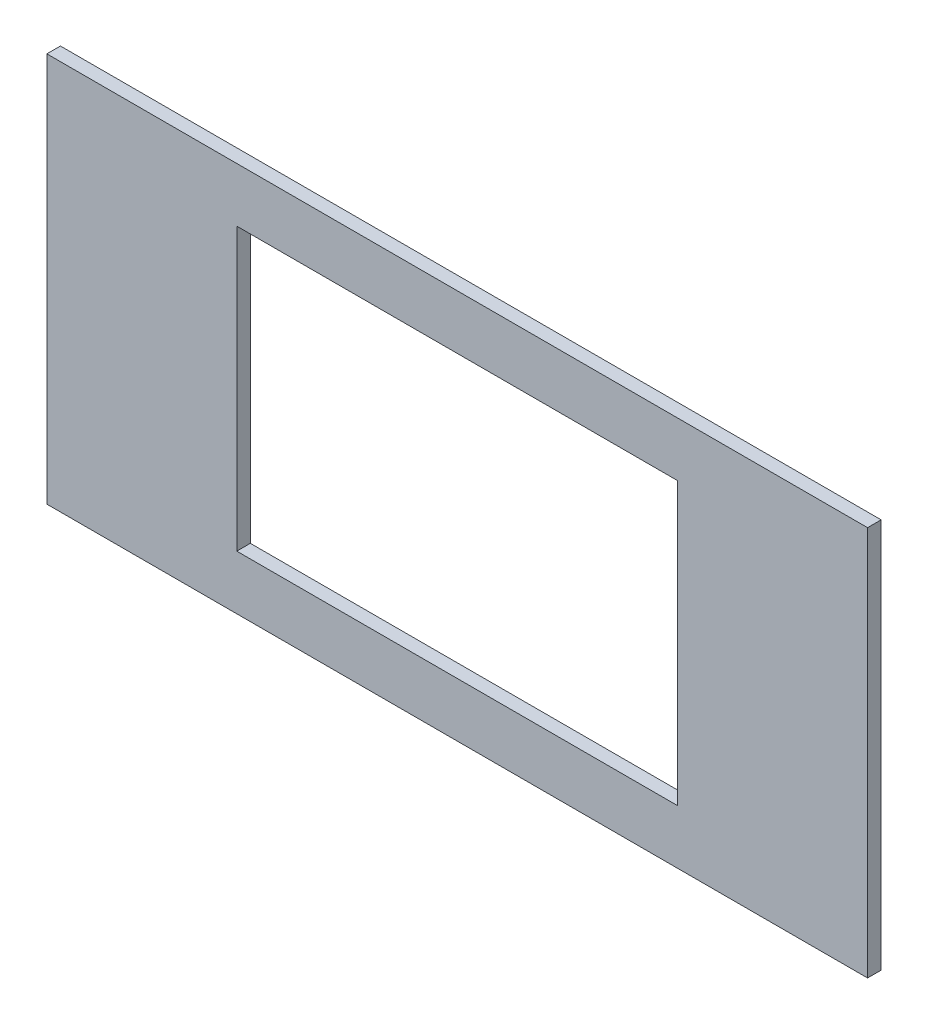
SolidWorks part; units mm, degrees
ref_plane "前视基准面" through (0, 0, 0) normal (0, 0, 1) x (1, 0, 0)
ref_plane "上视基准面" through (0, 0, 0) normal (0, 1, 0) x (1, 0, 0)
ref_plane "右视基准面" through (0, 0, 0) normal (1, 0, 0) x (0, 0, -1)
other "Configuration Table"
sketch "草图1" plane through (0, 0, 0) normal (0, 0, 1) x (1, 0, 0)
  line L1 (-99.0399, 66.2096) -> (142.9601, 66.2096)
  line L2 (-99.0399, 66.2096) -> (-99.0399, -48.7904)
  line L3 (-99.0399, -48.7904) -> (142.9601, -48.7904)
  line L4 (142.9601, 66.2096) -> (142.9601, -48.7904)
  line L5 (-43.0399, 50.2096) -> (86.9601, 50.2096)
  line L6 (-43.0399, 50.2096) -> (-43.0399, -32.7904)
  line L7 (-43.0399, -32.7904) -> (86.9601, -32.7904)
  line L8 (86.9601, 50.2096) -> (86.9601, -32.7904)
  dimension "D1" = 242
  dimension "D2" = 115
  dimension "D3" = 130
  dimension "D4" = 56
  dimension "D5" = 83
  dimension "D7" = 16
  dimension "D8" = 56
extrude "凸台-拉伸1" add sketch "草图1" along normal blind 4
